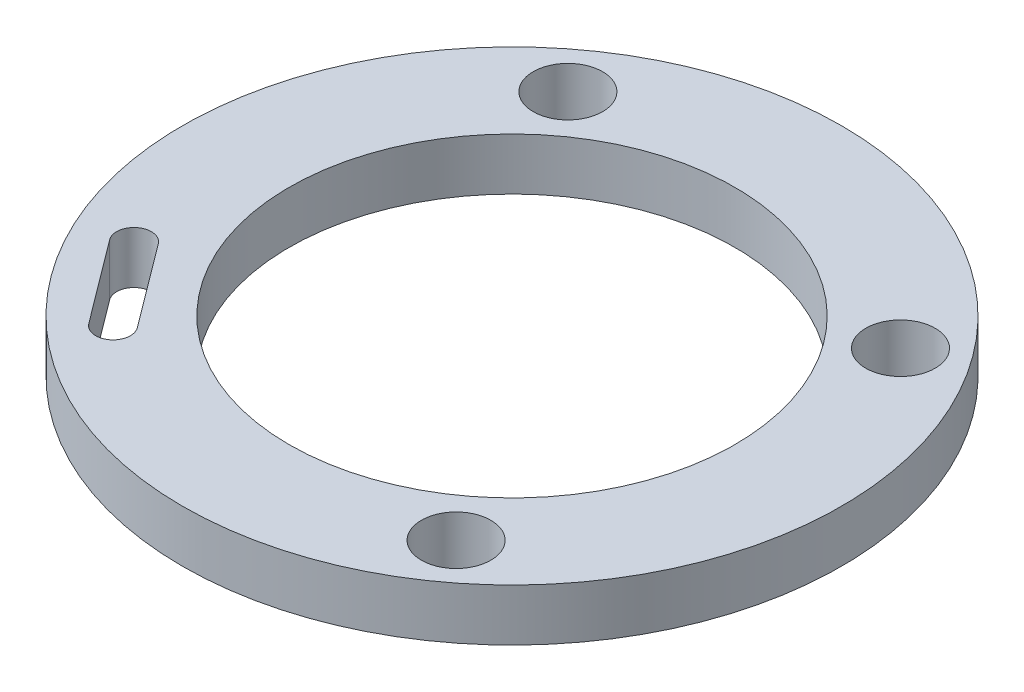
SolidWorks part; units mm, degrees
ref_plane "Front Plane" through (0, 0, 0) normal (0, 0, 1) x (1, 0, 0)
ref_plane "Top Plane" through (0, 0, 0) normal (0, 1, 0) x (1, 0, 0)
ref_plane "Right Plane" through (0, 0, 0) normal (1, 0, 0) x (0, 0, -1)
sketch "Sketch1" plane through (0, 0, 0) normal (0, 1, 0) x (1, 0, 0)
  line L0 (-11.0122, -11.9888) -> (-14.6073, -7.1851) construction
  line L1 (-11.8129, -12.5879) -> (-15.408, -7.7843)
  line L2 (-10.2116, -11.3896) -> (-13.8067, -6.5859)
  line L3 (-12.8098, -9.5869) -> (0, 0) construction
  line L4 (0, 0) -> (9.5869, -12.8098) construction
  line L5 (0, 0) -> (12.8098, 9.5869) construction
  line L6 (0, 0) -> (-9.5869, 12.8098) construction
  circle A0 centre (0, 0) radius 19
  circle A1 centre (0, 0) radius 12.85
  circle A2 centre (-9.5869, 12.8098) radius 2
  circle A3 centre (12.8098, 9.5869) radius 2
  circle A4 centre (9.5869, -12.8098) radius 2
  arc A5 (-11.8129, -12.5879) -> (-10.2116, -11.3896) centre (-11.0122, -11.9888) ccw
  circle A6 centre (-12.8098, -9.5869) radius 2 [skipped]
  arc A7 (-13.8067, -6.5859) -> (-15.408, -7.7843) centre (-14.6073, -7.1851) ccw
  point P8 (-12.8098, -9.5869)
  point P15 (0, 0)
  dimension "D1" = 38
  dimension "D2" = 25.7
  dimension "D3" = 4
  dimension "D4" = 16
  dimension "D6" = 16
  dimension "D7" = 3
  dimension "D8" = 2
  dimension "D5" = 4
extrude "Boss-Extrude1" add sketch "Sketch1" along normal blind 3
